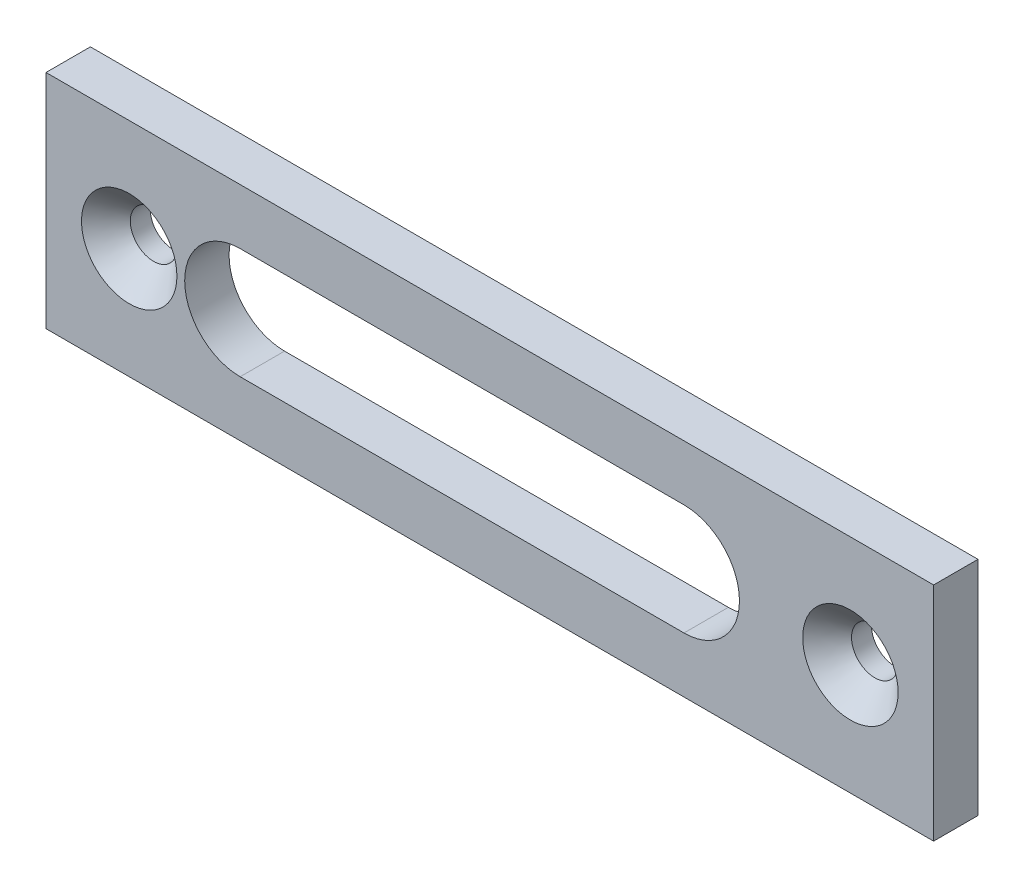
SolidWorks part; units mm, degrees
ref_plane "Plan de face" through (0, 0, 0) normal (0, 0, 1) x (1, 0, 0)
ref_plane "Plan de dessus" through (0, 0, 0) normal (0, 1, 0) x (1, 0, 0)
ref_plane "Plan de droite" through (0, 0, 0) normal (1, 0, 0) x (0, 0, -1)
sketch "Esquisse1" plane through (0, 0, 0) normal (0, 0, 1) x (1, 0, 0)
  line L0 (0, 10) -> (0, 0) construction
  line L1 (-40, 10) -> (40, 10)
  line L2 (-40, 10) -> (-40, -10)
  line L3 (-40, -10) -> (40, -10)
  line L4 (40, 10) -> (40, -10)
  line L5 (0, 0) -> (-40, 0) construction
  line L6 (0, 0) -> (32.5, 0) construction
  line L7 (-22.5, 5) -> (17.5, 5)
  line L8 (-22.5, -5) -> (17.5, -5)
  circle A0 centre (-32.5, 0) radius 2.1
  circle A1 centre (32.5, 0) radius 2.1
  arc A2 (-22.5, 5) -> (-22.5, -5) centre (-22.5, 0) ccw
  arc A3 (17.5, -5) -> (17.5, 5) centre (17.5, 0) ccw
  dimension "D3" = 4.2
  dimension "D4" = 65
  dimension "D6" = 10
  dimension "D7" = 40
  dimension "D8" = 17.5
  dimension "D1" = 80
  dimension "D2" = 20
  dimension "D5" = 32.5
extrude "Extrusion1" add sketch "Esquisse1" along normal blind 4
chamfer "Chanfrein1" distance 2.2 angle 45 2 edges at (-30.4, 0, 4) (34.6, 0, 4)
